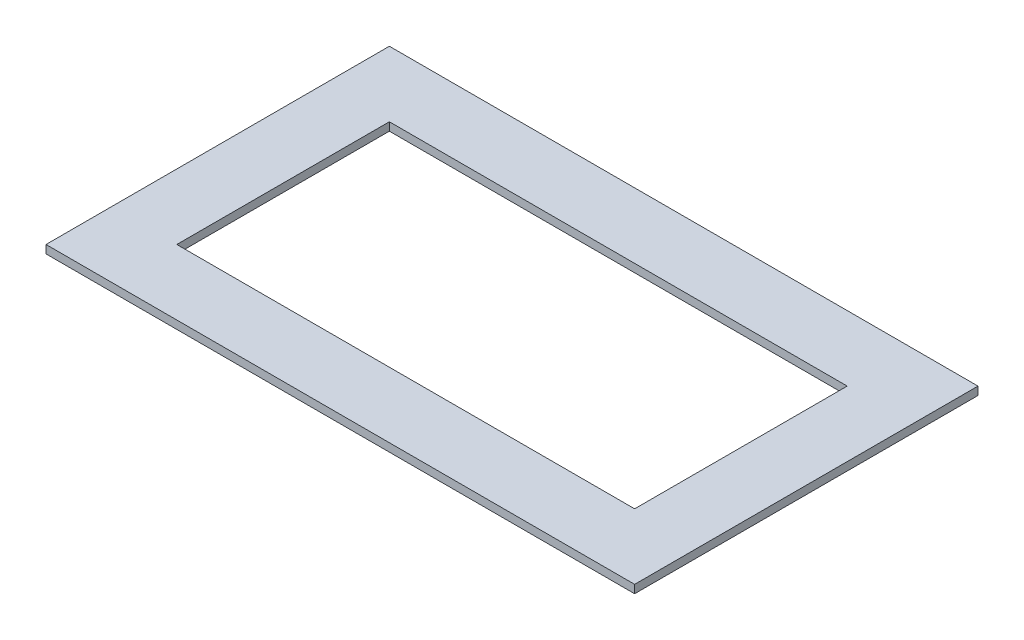
SolidWorks part; units mm, degrees
material "AISI 1020"
ref_plane "Front Plane" through (0, 0, 0) normal (0, 0, 1) x (1, 0, 0)
ref_plane "Top Plane" through (0, 0, 0) normal (0, 1, 0) x (1, 0, 0)
ref_plane "Right Plane" through (0, 0, 0) normal (1, 0, 0) x (0, 0, -1)
sketch "Sketch1" plane through (0, 0, 0) normal (0, 1, 0) x (1, 0, 0)
  line L1 (-180, -105) -> (180, -105)
  line L2 (-180, -105) -> (-180, 105)
  line L3 (-180, 105) -> (180, 105)
  line L4 (180, -105) -> (180, 105)
  line L5 (-180, -105) -> (180, 105) construction
  line L6 (-180, 105) -> (180, -105) construction
  line L7 (-140, -65) -> (140, -65)
  line L8 (-140, -65) -> (-140, 65)
  line L9 (-140, 65) -> (140, 65)
  line L10 (140, -65) -> (140, 65)
  line L11 (-140, -65) -> (140, 65) construction
  line L12 (-140, 65) -> (140, -65) construction
  point P0 (0, 0)
  point P6 (0, 0)
  dimension "D1" = 360
  dimension "D2" = 210
  dimension "D3" = 280
  dimension "D4" = 130
  dimension "D5" = 40
  dimension "D6" = 40
extrude "Boss-Extrude1" add sketch "Sketch1" along normal blind 5
